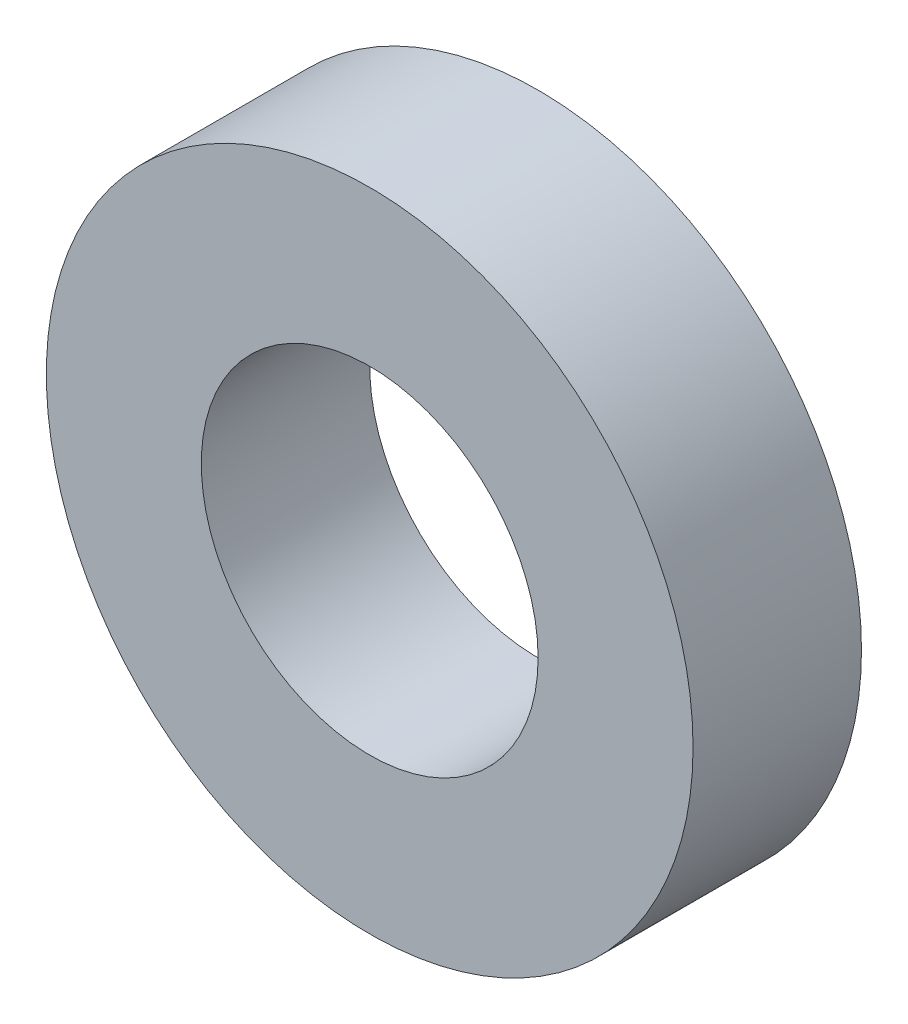
SolidWorks part; units mm, degrees
ref_plane "Front Plane" through (0, 0, 0) normal (0, 0, 1) x (1, 0, 0)
ref_plane "Top Plane" through (0, 0, 0) normal (0, 1, 0) x (1, 0, 0)
ref_plane "Right Plane" through (0, 0, 0) normal (1, 0, 0) x (0, 0, -1)
sketch "Sketch1" plane through (0, 0, 0) normal (0, 0, 1) x (1, 0, 0)
  circle A0 centre (0, 0) radius 9.6
  dimension "D1" = 19.2
extrude "Boss-Extrude1" add sketch "Sketch1" along normal blind 5
sketch "Sketch2" plane through (0, 0, 5) normal (0, 0, 1) x (1, 0, 0)
  circle A0 centre (0, 0) radius 5
  dimension "D1" = 10
extrude "Cut-Extrude1" cut sketch "Sketch2" against normal blind 5
